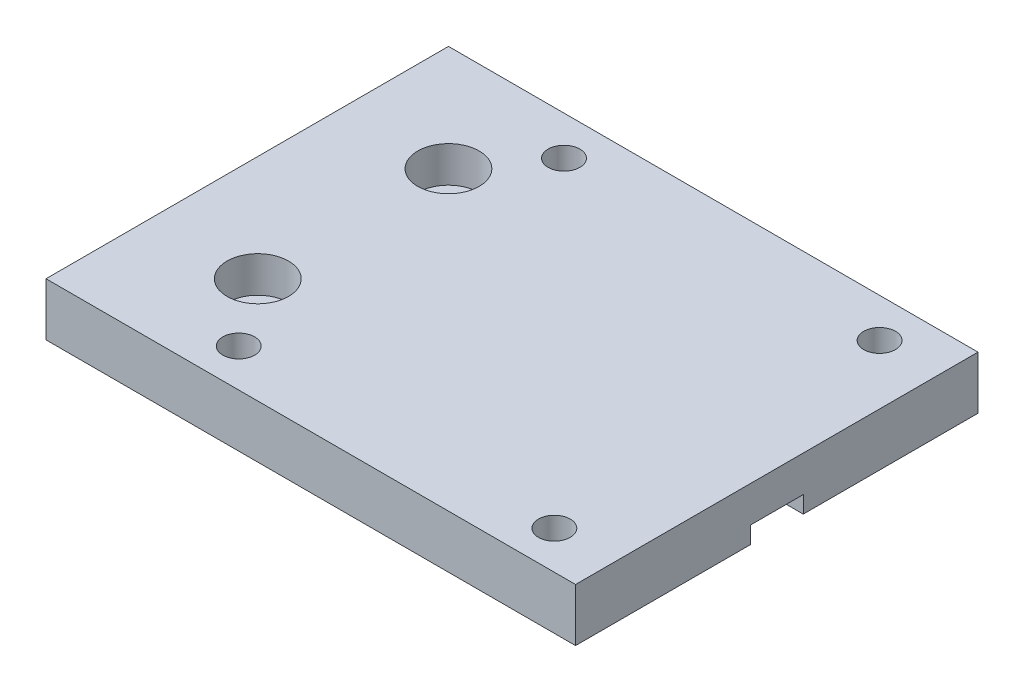
SolidWorks part; units mm, degrees
ref_plane "Front Plane" through (0, 0, 0) normal (0, 0, 1) x (1, 0, 0)
ref_plane "Top Plane" through (0, 0, 0) normal (0, 1, 0) x (1, 0, 0)
ref_plane "Right Plane" through (0, 0, 0) normal (1, 0, 0) x (0, 0, -1)
sketch "Sketch1" plane through (0, 0, 0) normal (0, 1, 0) x (1, 0, 0)
  line L1 (-31.75, 24.13) -> (31.75, 24.13)
  line L2 (-31.75, 24.13) -> (-31.75, -24.13)
  line L3 (-31.75, -24.13) -> (31.75, -24.13)
  line L4 (31.75, 24.13) -> (31.75, -24.13)
  line L5 (-31.75, 24.13) -> (31.75, -24.13) construction
  line L6 (-31.75, -24.13) -> (31.75, 24.13) construction
  point P0 (0, 0)
  dimension "D1" = 48.26
  dimension "D2" = 63.5
extrude "Boss-Extrude1" add sketch "Sketch1" against normal blind 6.35
sketch "Sketch2" plane through (0, 0, 0) normal (0, 1, 0) x (1, 0, 0)
  line L0 (-31.75, 24.13) -> (-31.75, -24.13) construction
  circle A0 centre (-19.05, 11.43) radius 3.683
  dimension "D1" = 7.366
  dimension "D2" = 12.7
  dimension "D6" = 11.43
extrude "Cut-Extrude1" cut sketch "Sketch2" against normal blind 4.318
sketch "Sketch3" plane through (0, -4.318, 0) normal (0, 1, 0) x (1, 0, 0)
  circle A0 centre (-19.05, 11.43) radius 2.159
  dimension "D1" = 4.318
extrude "Cut-Extrude2" cut sketch "Sketch3" against normal blind 4.318
sketch "Sketch5" plane through (0, -6.35, 0) normal (0, -1, 0) x (1, 0, 0)
  line L0 (31.75, 24.13) -> (31.75, -24.13) construction
  line L1 (-15.24, -3.175) -> (31.75, -3.175)
  line L3 (-15.24, 3.175) -> (31.75, 3.175)
  line L4 (31.75, -3.175) -> (31.75, 3.175)
  line L5 (-15.24, -1.524) -> (31.75, 3.175) construction
  line L6 (-15.24, 1.524) -> (31.75, -3.175) construction
  line L7 (-15.24, -3.175) -> (-15.24, 3.175)
  point P0 (0, 0)
  dimension "D1" = 6.35
  dimension "D2" = 46.99
  dimension "D3" = 3.175
extrude "Cut-Extrude3" cut sketch "Sketch5" against normal blind 2.032
sketch "Sketch4" plane through (0, 0, 0) normal (0, 1, 0) x (1, 0, 0)
  line L0 (-31.75, 24.13) -> (-31.75, -24.13) construction
  circle A0 centre (-13.208, -19.558) radius 1.905
  circle A1 centre (-13.208, 19.442) radius 1.905
  circle A2 centre (24.638, -19.558) radius 1.905
  circle A3 centre (24.638, 19.442) radius 1.905
  dimension "D2" = 3.81
  dimension "D3" = 3.81
  dimension "D6" = 3.81
  dimension "D7" = 3.81
  dimension "D1" = 18.542
  dimension "D4" = 39
  dimension "D5" = 19.558
  dimension "D8" = 37.846
extrude "Cut-Extrude4" cut sketch "Sketch4" against normal blind 14.732
mirror "Mirror1" about plane through (0, 0, 0) normal (0, 0, 1) of "Cut-Extrude2", "Cut-Extrude1"
